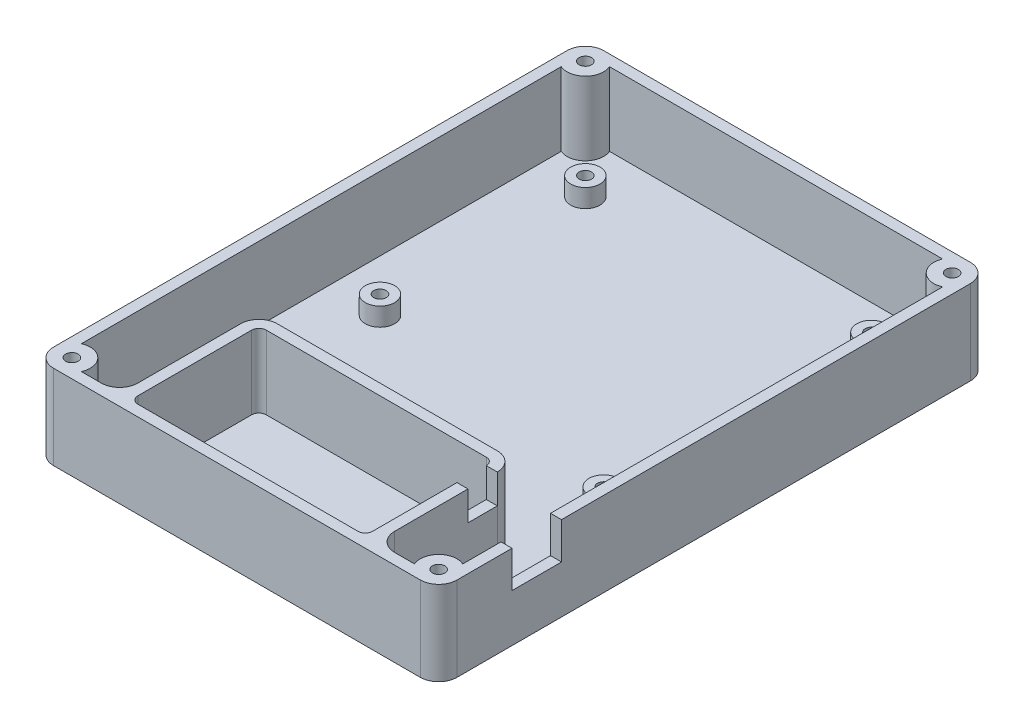
SolidWorks part; units mm, degrees
ref_plane "Plano frontal" through (0, 0, 0) normal (0, 0, 1) x (1, 0, 0)
ref_plane "Plano superior" through (0, 0, 0) normal (0, 1, 0) x (1, 0, 0)
ref_plane "Plano direito" through (0, 0, 0) normal (1, 0, 0) x (0, 0, -1)
sketch "Esboço1" plane through (0, 0, 0) normal (0, 1, 0) x (1, 0, 0)
  line L1 (-55, -75) -> (55, -75)
  line L2 (-55, -75) -> (-55, 75)
  line L3 (-55, 75) -> (55, 75)
  line L4 (55, -75) -> (55, 75)
  line L5 (-55, -75) -> (55, 75) construction
  line L6 (-55, 75) -> (55, -75) construction
  line L10 (0, 0) -> (0, 50000) construction
  point P0 (0, 0)
  dimension "D1" = 150
  dimension "D2" = 110
extrude "Ressalto-extrusão3" add sketch "Esboço1" along normal blind 23
fillet "Filete2" radius 5 4 edges at (-55, 11.5, -75) (55, 11.5, -75) (55, 11.5, 75) (-55, 11.5, 75)
shell "Casca1" thickness 3
sketch "Esboço14" plane through (0, 3, 0) normal (0, 1, 0) x (1, 0, 0)
  arc A1 (-55, -70) -> (-50, -75) centre (-50, -70) ccw construction
  circle A2 centre (-50, -70) radius 5
  circle A3 centre (50, -70) radius 5
  circle A4 centre (50, 70) radius 5
  circle A5 centre (-50, 70) radius 5
  arc A6 (50, -75) -> (55, -70) centre (50, -70) ccw construction
  arc A7 (55, 70) -> (50, 75) centre (50, 70) ccw construction
  arc A8 (-50, 75) -> (-55, 70) centre (-50, 70) ccw construction
extrude "Ressalto-extrusão7" add sketch "Esboço14" along normal up to surface (20 mm away) up to face at (0, 23, 0)
sketch "Esboço6" plane through (0, 0, 0) normal (0, 1, 0) x (1, 0, 0)
  line L0 (-45.4174, -72) -> (45.4174, -72) construction
  line L1 (-32, -37) -> (32, -37)
  line L2 (-32, -37) -> (-32, -72)
  line L4 (32, -37) -> (32, -72)
  line L5 (-32, -37) -> (32, -72) construction
  line L6 (-32, -72) -> (32, -37) construction
  line L7 (-45.4174, -72) -> (45.4174, -72) construction
  line L14 (-35, -34) -> (-35, -72)
  line L15 (-35, -34) -> (35, -34)
  line L16 (35, -34) -> (35, -72)
  line L17 (-35, -72) -> (-32, -72)
  line L18 (35, -72) -> (32, -72)
  point P0 (0, -54.5)
  dimension "D1" = 64
  dimension "D2" = 35
  dimension "D3" = 3
extrude "Ressalto-extrusão4" add sketch "Esboço6" along normal up to surface (23 mm away) up to face at (0, 23, 0)
fillet "Filete6" radius 2 4 edges at (-32, 13, 72) (-32, 13, 37) (32, 13, 72) (32, 13, 37)
fillet "Filete8" radius 5 4 edges at (35, 13, 72) (35, 13, 34) (-35, 13, 34) (-35, 13, 72)
sketch "Esboço7" plane through (0, 23, 0) normal (0, 1, 0) x (1, 0, 0)
  line L0 (35, -67) -> (35, -39) construction
  line L1 (32, -39) -> (35, -39)
  line L2 (32, -39) -> (32, -47)
  line L3 (32, -47) -> (35, -47)
  line L4 (35, -39) -> (35, -47)
  dimension "D1" = 8
extrude "Corte-extrusão1" cut sketch "Esboço7" against normal blind 8
sketch "Esboço8" plane through (0, 23, 0) normal (0, 1, 0) x (1, 0, 0)
  line L0 (52, -65.4174) -> (52, 65.4174) construction
  line L1 (52, -41.5) -> (55, -41.5)
  line L2 (52, -41.5) -> (52, -55)
  line L3 (52, -55) -> (55, -55)
  line L4 (55, -41.5) -> (55, -55)
  line L5 (55, -70) -> (55, 70) construction
  line L6 (-50, -75) -> (50, -75) construction
  dimension "D1" = 13.5
  dimension "D2" = 20
extrude "Corte-extrusão2" cut sketch "Esboço8" against normal blind 10
sketch "Esboço17" plane through (0, 3, 0) normal (0, 1, 0) x (1, 0, 0)
  line L0 (52, -41.5) -> (52, 65.4174) construction
  line L4 (30, -34) -> (-30, -34) construction
  line L5 (-52, 65.4174) -> (-52, -65.4174) construction
  line L6 (-52, 65.4174) -> (-52, -65.4174) construction
  line L7 (45.4174, 72) -> (-45.4174, 72) construction
  circle A0 centre (-38, 58) radius 4
  circle A1 centre (-38, 2) radius 4
  circle A2 centre (38, -13) radius 4
  circle A3 centre (38, 60) radius 4
  dimension "D1" = 8
  dimension "D2" = 8
  dimension "D3" = 8
  dimension "D4" = 8
  dimension "D8" = 36
  dimension "D9" = 21
  dimension "D6" = 14
  dimension "D10" = 14
  dimension "D5" = 14
  dimension "D7" = 14
  dimension "D11" = 12
extrude "Ressalto-extrusão8" add sketch "Esboço17" along normal blind 5
hole_wizard "Escareado para parafuso de máquina com cabeça chata de M33" positions "Esboço18" profile "Esboço19" countersink size "M3" standard "Ansi Metric"
sketch "Esboço18" plane through (0, 0, 0) normal (0, -1, 0) x (-1, 0, 0)
  point P0 (-38, -13)
  point P3 (38, 2)
  point P6 (38, 58)
  point P9 (-38, 60)
sketch "Esboço19" plane through (38, 0, 13) normal (1, 0, 0) x (0, 0, -1)
  line L0 (0, 0) -> (0, 16.0215)
  line L1 (0, 16.0215) -> (1.7, 15)
  line L2 (1.7, 15) -> (1.7, 1.45)
  line L3 (1.7, 1.45) -> (3.15, 0)
  line L5 (3.15, 0) -> (0, 0)
  line L6 (-1.7, 1.45) -> (-3.15, 0) construction
  line L10 (0, 16.0215) -> (-1.7, 15) construction
  line L11 (0, -6.35) -> (0, 107.95) construction
  dimension "Hole Dia." = 3.4
  dimension "Hole Depth" = 15
  dimension "Near C'Sink Dia." = 6.3
  dimension "Near C'Sink Angle" = 90
  dimension "Drill Angle" = 118
hole_wizard "Escareado para parafuso de máquina com cabeça chata de M32" positions "Esboço15" profile "Esboço16" countersink size "M3" standard "Ansi Metric"
sketch "Esboço15" plane through (0, 0, 0) normal (0, -1, 0) x (-1, 0, 0)
  point P0 (50, -70)
  point P3 (-50, -70)
  point P6 (-50, 70)
  point P9 (50, 70)
sketch "Esboço16" plane through (-50, 0, 70) normal (1, 0, 0) x (0, 0, -1)
  line L0 (0, 0) -> (0, 24.0205)
  line L1 (0, 24.0205) -> (1.7, 22.999)
  line L2 (1.7, 22.999) -> (1.7, 1.45)
  line L3 (1.7, 1.45) -> (3.15, 0)
  line L5 (3.15, 0) -> (0, 0)
  line L6 (-1.7, 1.45) -> (-3.15, 0) construction
  line L10 (0, 24.0205) -> (-1.7, 22.999) construction
  line L11 (0, -6.35) -> (0, 107.95) construction
  dimension "Hole Dia." = 3.4
  dimension "Hole Depth" = 22.999
  dimension "Near C'Sink Dia." = 6.3
  dimension "Near C'Sink Angle" = 90
  dimension "Drill Angle" = 118
equation "\"D_BasePCB\"= 8mm"
equation "\"D1@Esboço17\"=\"D_BasePCB\""
equation "\"D2@Esboço17\"=\"D_BasePCB\""
equation "\"D3@Esboço17\"=\"D_BasePCB\""
equation "\"D4@Esboço17\"=\"D_BasePCB\""
equation "\"D8@Esboço17\"=36"
